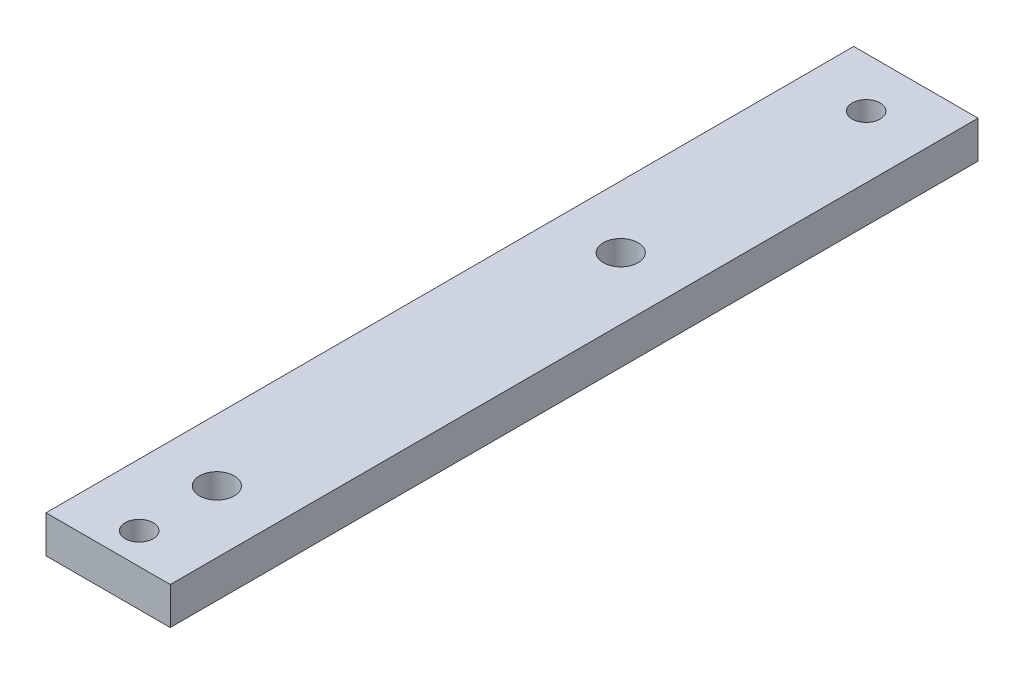
SolidWorks part; units mm, degrees
ref_plane "정면" through (0, 0, 0) normal (0, 0, 1) x (1, 0, 0)
ref_plane "윗면" through (0, 0, 0) normal (0, 1, 0) x (1, 0, 0)
ref_plane "우측면" through (0, 0, 0) normal (1, 0, 0) x (0, 0, -1)
sketch "스케치1" plane through (0, 0, 0) normal (0, 1, 0) x (1, 0, 0)
  line L0 (3.913, -50.5435) -> (3.913, -45.5435) construction
  line L1 (-6.087, 14.4565) -> (3.913, 14.4565)
  line L2 (-6.087, 14.4565) -> (-6.087, -50.5435)
  line L3 (-6.087, -50.5435) -> (3.913, -50.5435)
  line L4 (3.913, 14.4565) -> (3.913, -50.5435)
  line L5 (3.913, -45.5435) -> (-6.087, -45.5435) construction
  line L6 (3.913, -45.5435) -> (3.913, -5.5435) construction
  line L7 (3.913, -5.5435) -> (-6.087, -5.5435) construction
  circle A0 centre (-1.087, -9.2935) radius 1.4
  circle A1 centre (-1.087, -41.7935) radius 1.4
  circle A2 centre (-1.087, 10.4565) radius 1.125
  circle A3 centre (-1.087, -48.0435) radius 1.125
  point P11 (-1.087, -45.5435)
  point P17 (-1.087, -50.5435)
  dimension "D5" = 2.8
  dimension "D7" = 5
  dimension "D8" = 2.8
  dimension "D11" = 2.25
  dimension "D12" = 2.25
  dimension "D1" = 10
  dimension "D2" = 65
  dimension "D3" = 5
  dimension "D4" = 40
  dimension "D6" = 3.75
  dimension "D9" = 3.75
  dimension "D10" = 5
  dimension "D13" = 4
  dimension "D14" = 2.5
extrude "보스-돌출1" add sketch "스케치1" along normal blind 3
